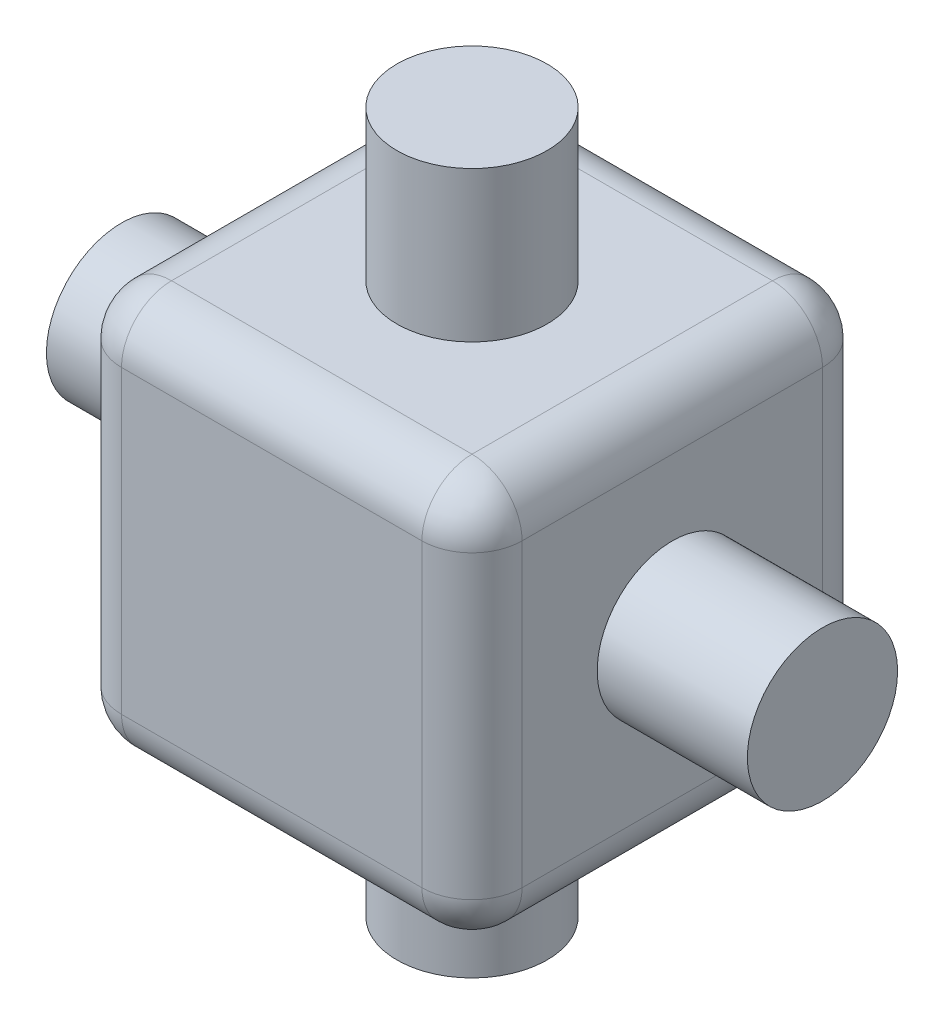
SolidWorks part; units mm, degrees
ref_plane "Front Plane" through (0, 0, 0) normal (0, 0, 1) x (1, 0, 0)
ref_plane "Top Plane" through (0, 0, 0) normal (0, 1, 0) x (1, 0, 0)
ref_plane "Right Plane" through (0, 0, 0) normal (1, 0, 0) x (0, 0, -1)
sketch "Sketch1" plane through (0, 0, 0) normal (0, 0, 1) x (1, 0, 0)
  line L1 (4, -4) -> (-4, -4)
  line L2 (4, -4) -> (4, 4)
  line L3 (4, 4) -> (-4, 4)
  line L4 (-4, -4) -> (-4, 4)
  line L5 (4, -4) -> (-4, 4) construction
  line L6 (4, 4) -> (-4, -4) construction
  point P0 (0, 0)
  dimension "D1" = 8
extrude "Boss-Extrude1" add sketch "Sketch1" along normal blind 8
sketch "Sketch2" plane through (0, 4, 0) normal (0, 1, 0) x (1, 0, 0)
  line L0 (0, 0) -> (0, -8) construction
  line L1 (4, -8) -> (-4, -8) construction
  line L2 (-4, -4) -> (4, -4) construction
  line L3 (-4, -8) -> (-4, 0) construction
  line L4 (4, -8) -> (4, 0) construction
  circle A0 centre (0, -4) radius 1.5
  dimension "D1" = 3
extrude "Boss-Extrude2" add sketch "Sketch2" along normal blind 3
sketch "Sketch3" plane through (4, 0, 0) normal (1, 0, 0) x (0, 0, -1)
  line L0 (-4, 4) -> (-4, -4) construction
  line L1 (-8, 4) -> (0, 4) construction
  line L2 (-8, -4) -> (0, -4) construction
  circle A0 centre (-4, 0) radius 1.5
  dimension "D1" = 3
extrude "Boss-Extrude3" add sketch "Sketch3" along normal blind 3
sketch "Sketch4" plane through (0, -4, 0) normal (0, -1, 0) x (1, 0, 0)
  line L0 (-4, 4) -> (4, 4) construction
  line L1 (-4, 8) -> (-4, 0) construction
  line L2 (4, 8) -> (4, 0) construction
  circle A0 centre (0, 4) radius 1.5
  dimension "D1" = 3
extrude "Boss-Extrude4" add sketch "Sketch4" along normal blind 3
sketch "Sketch5" plane through (-4, 0, 0) normal (-1, 0, 0) x (0, 0, 1)
  line L0 (4, 4) -> (4, -4) construction
  line L1 (8, 4) -> (0, 4) construction
  line L2 (2.5, -4) -> (5.5, -4) construction
  circle A0 centre (4, 0) radius 1.5
  dimension "D1" = 3
extrude "Boss-Extrude5" add sketch "Sketch5" along normal blind 3
fillet "Fillet3" radius 1 1 edges at (4, 0, 0)
fillet "Fillet4" radius 1 1 edges at (-4, 0, 0)
fillet "Fillet5" radius 1 1 edges at (-4, 0, 8)
fillet "Fillet6" radius 1 1 edges at (4, 0, 8)
fillet "Fillet7" radius 1 8 edges at (3.7071, -4, 0.2929) (0, -4, 0) (-3.7071, -4, 0.2929) (-4, -4, 4) (0, -4, 8) (-3.7071, -4, 7.7071) (4, -4, 4) (3.7071, -4, 7.7071)
fillet "Fillet8" radius 1 8 edges at (0, 4, 0) (3.7071, 4, 0.2929) (-3.7071, 4, 0.2929) (-4, 4, 4) (-3.7071, 4, 7.7071) (0, 4, 8) (4, 4, 4) (3.7071, 4, 7.7071)
